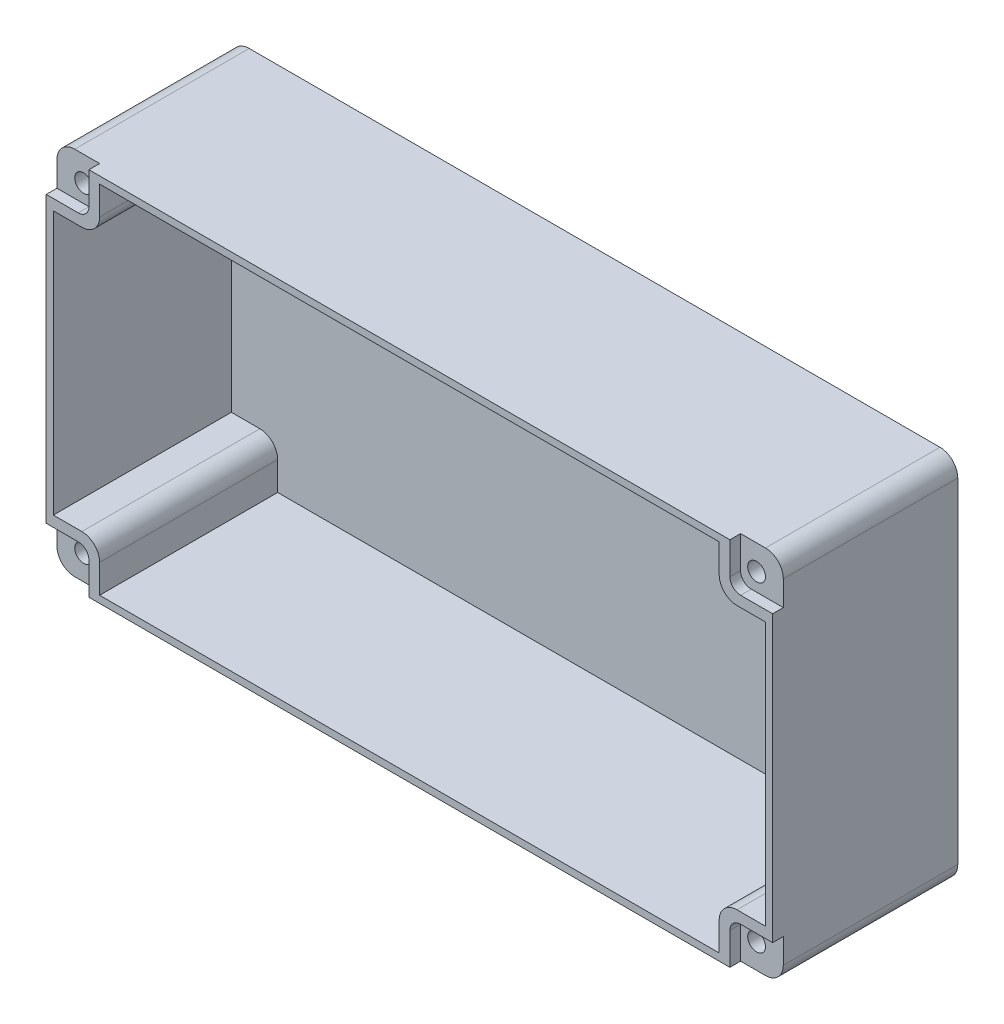
SolidWorks part; units mm, degrees
ref_plane "Plano frontal" through (0, 0, 0) normal (0, 0, 1) x (1, 0, 0)
ref_plane "Plano superior" through (0, 0, 0) normal (0, 1, 0) x (1, 0, 0)
ref_plane "Plano direito" through (0, 0, 0) normal (1, 0, 0) x (0, 0, -1)
sketch "Esboço1" plane through (0, 0, 0) normal (0, 0, 1) x (1, 0, 0)
  line L1 (-102, 52) -> (102, 52)
  line L2 (-102, 52) -> (-102, -52)
  line L3 (-102, -52) -> (102, -52)
  line L4 (102, 52) -> (102, -52)
  line L5 (-102, 52) -> (102, -52) construction
  line L6 (-102, -52) -> (102, 52) construction
  point P0 (0, 0)
  dimension "D1" = 204
  dimension "D2" = 104
extrude "Ressalto-extrusão1" add sketch "Esboço1" against normal blind 52
sketch "Esboço2" plane through (0, 0, 0) normal (0, 0, 1) x (1, 0, 0)
  line L0 (0, 50) -> (0, -50) construction
  line L1 (-87, 50) -> (87, 50)
  line L2 (-100, 37) -> (-100, -37)
  line L3 (-87, -50) -> (87, -50)
  line L4 (100, 37) -> (100, -37)
  line L5 (102, -52) -> (102, 52) construction
  line L6 (-102, -52) -> (102, -52) construction
  line L9 (100, -37) -> (92, -37)
  line L10 (87, -50) -> (87, -42)
  line L11 (0, 0) -> (43.167, 0) construction
  line L12 (-87, 50) -> (-100, 50) construction
  line L13 (-87, -50) -> (-87, -42)
  line L14 (-100, -37) -> (-92, -37)
  line L15 (102, 52) -> (-102, 52) construction
  line L16 (-102, 52) -> (-102, -52) construction
  line L17 (-100, 50) -> (-100, 37) construction
  line L18 (-100, 43.5) -> (-87, 43.5) construction
  line L19 (100, 37) -> (92, 37)
  line L20 (87, 50) -> (87, 42)
  line L21 (-87, 50) -> (-87, 42)
  line L22 (-100, 37) -> (-92, 37)
  arc A0 (87, 42) -> (92, 37) centre (92, 42) ccw
  arc A1 (92, -37) -> (87, -42) centre (92, -42) ccw
  arc A2 (-87, -42) -> (-92, -37) centre (-92, -42) ccw
  arc A3 (-87, 42) -> (-92, 37) centre (-92, 42) cw
  point P0 (0, 0)
  point P21 (87, 37)
  point P26 (87, -37)
  point P29 (-87, -37)
  point P32 (-87, 37)
  dimension "D1" = 5
  dimension "D2" = 2
  dimension "D3" = 13
  dimension "D4" = 13
  dimension "D5" = 2
  dimension "D6" = 2
  dimension "D7" = 2
extrude "Corte-extrusão1" cut sketch "Esboço2" against normal blind 50
ref_plane "Plano Posterior" through (0, 0, -52) normal (0, 0, -1) x (-1, 0, 0)
fillet "Filete1" radius 5 4 edges at (-102, 52, -26) (-102, -52, -26) (102, -52, -26) (102, 52, -26)
sketch "Esboço4" plane through (0, 0, -52) normal (0, 0, -1) x (-1, 0, 0)
  line L0 (-102, -47) -> (-102, 47) construction
  line L1 (-102, 52) -> (102, 52) construction
  line L2 (-102, 52) -> (-102, -52) construction
  line L3 (-102, -52) -> (102, -52) construction
  line L4 (102, 52) -> (102, -52) construction
  line L5 (-102, 52) -> (102, -52) construction
  line L6 (-102, -52) -> (102, 52) construction
  line L7 (-97, 52) -> (97, 52) construction
  line L8 (0, 52) -> (0, -52) construction
  line L9 (-97, 50) -> (-90, 50)
  line L10 (-100, 47) -> (-100, 40)
  line L11 (-100, 40) -> (-93, 40)
  line L12 (-90, 50) -> (-90, 43)
  line L13 (-102, 0) -> (102, 0) construction
  arc A0 (-90, 43) -> (-93, 40) centre (-93, 43) cw
  arc A1 (-97, 50) -> (-100, 47) centre (-97, 47) ccw
  point P0 (0, 0)
  point P16 (-90, 40)
  point P19 (-100, 50)
  dimension "D7" = 3
  dimension "D1" = 0
  dimension "D2" = 0
  dimension "D3" = 4
  dimension "D4" = 4
  dimension "D5" = 10
  dimension "D6" = 10
extrude "Corte-extrusão2" cut sketch "Esboço4" against normal blind 40
sketch "Esboço7" plane through (0, 0, 0) normal (0, 0, 1) x (1, 0, 0)
  line L0 (-102, 40) -> (-93, 40)
  line L1 (-102, 52.75) -> (102, 52.75) construction
  line L2 (-102, 52.75) -> (-102, -52.75) construction
  line L3 (-102, -52.75) -> (102, -52.75) construction
  line L4 (102, 52.75) -> (102, -52.75) construction
  line L5 (-102, 52.75) -> (102, -52.75) construction
  line L6 (-102, -52.75) -> (102, 52.75) construction
  line L7 (-90, 43) -> (-90, 52)
  line L8 (0, 52.75) -> (0, -52.75) construction
  line L9 (-97, 52) -> (-90, 52)
  line L10 (-102, 47) -> (-102, 40)
  line L13 (-102, 0) -> (102, 0) construction
  arc A1 (-97, 52) -> (-102, 47) centre (-97, 47) ccw
  arc A2 (-97, 52) -> (-102, 47) centre (-97, 47) ccw construction
  arc A3 (-90, 43) -> (-93, 40) centre (-93, 43) cw
  point P0 (0, 0)
  point P14 (-90, 40)
  point P16 (-90, 40)
  point P19 (-102, 52)
  dimension "D2" = 3
  dimension "D1" = 12
  dimension "D6" = 12
extrude "Corte-extrusão5" cut sketch "Esboço7" against normal blind 3
sketch "Esboço8" plane through (0, 0, 0) normal (0, 0, 1) x (1, 0, 0)
  line L0 (0, 0) -> (0, 69.2866) construction
  line L6 (-102, 40) -> (-93, 40) construction
  circle A4 centre (-94.5, 45) radius 2.5
  dimension "D1" = 5
  dimension "D2" = 5
  dimension "D3" = 94.5
extrude "Corte-extrusão6" cut sketch "Esboço8" against normal through all and the other way through all
mirror "Espelhar1" about plane through (0, 0, 0) normal (1, 0, 0) of "Corte-extrusão6", "Corte-extrusão2", "Corte-extrusão5"
mirror "Espelhar2" about plane through (0, 0, 0) normal (0, 1, 0) of "Espelhar1", "Corte-extrusão2", "Corte-extrusão5", "Corte-extrusão6"
